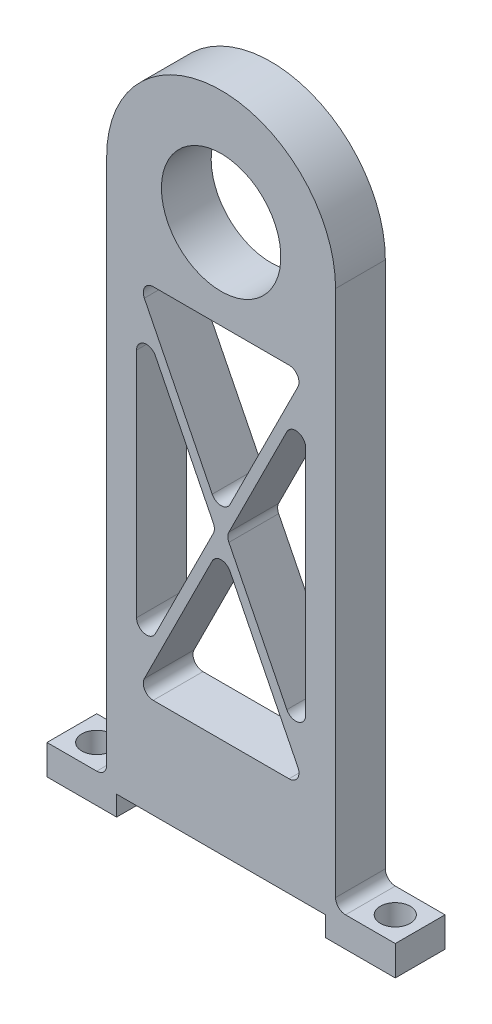
SolidWorks part; units mm, degrees
ref_plane "Front Plane" through (0, 0, 0) normal (0, 0, 1) x (1, 0, 0)
ref_plane "Top Plane" through (0, 0, 0) normal (0, 1, 0) x (1, 0, 0)
ref_plane "Right Plane" through (0, 0, 0) normal (1, 0, 0) x (0, 0, -1)
sketch "Sketch1" plane through (0, 0, 0) normal (0, 1, 0) x (1, 0, 0)
  line L1 (44.45, 6.35) -> (-44.45, 6.35)
  line L2 (44.45, 6.35) -> (44.45, -6.35)
  line L3 (44.45, -6.35) -> (-44.45, -6.35)
  line L4 (-44.45, 6.35) -> (-44.45, -6.35)
  line L5 (44.45, 6.35) -> (-44.45, -6.35) construction
  line L6 (44.45, -6.35) -> (-44.45, 6.35) construction
  line L7 (-38.1, 0) -> (-44.45, 0) construction
  line L8 (38.1, 0) -> (44.45, 0) construction
  circle A0 centre (-38.1, 0) radius 3.81
  circle A1 centre (38.1, 0) radius 3.81
  point P0 (0, 0)
  dimension "D1" = 7.62
  dimension "D2" = 76.2
  dimension "D3" = 88.9
  dimension "D4" = 12.7
extrude "Boss-Extrude1" add sketch "Sketch1" along normal blind 7.62
sketch "Sketch2" plane through (0, 7.62, 0) normal (0, 1, 0) x (1, 0, 0)
  line L0 (44.45, 6.35) -> (-44.45, 6.35) construction
  line L1 (29.21, 6.35) -> (-29.21, 6.35)
  line L2 (29.21, 6.35) -> (29.21, -6.35)
  line L3 (29.21, -6.35) -> (-29.21, -6.35)
  line L4 (-29.21, 6.35) -> (-29.21, -6.35)
  line L5 (29.21, 6.35) -> (-29.21, -6.35) construction
  line L6 (29.21, -6.35) -> (-29.21, 6.35) construction
  point P0 (0, 0)
  dimension "D1" = 58.42
extrude "Boss-Extrude2" add sketch "Sketch2" along normal blind 137.16
sketch "Sketch3" plane through (0, 0, 6.35) normal (0, 0, 1) x (1, 0, 0)
  line L0 (29.21, 144.78) -> (-29.21, 144.78)
  arc A0 (29.21, 144.78) -> (-29.21, 144.78) centre (0, 144.78) ccw
extrude "Boss-Extrude3" add sketch "Sketch3" against normal up to surface (12.7 mm away) contours A0 L0 up to face at (0, 40.005, -6.35)
sketch "Sketch4" plane through (0, 0, -6.35) normal (0, 0, -1) x (-1, 0, 0)
  line L0 (0, 144.78) -> (0, 0) construction
  line L1 (-44.45, 0) -> (44.45, 0) construction
  circle A0 centre (0, 144.78) radius 15.24
  dimension "D1" = 30.48
extrude "Cut-Extrude1" cut sketch "Sketch4" against normal up to surface (12.7 mm away) up to face at (0, 43.6562, 6.35)
sketch "Sketch5" plane through (0, 0, 6.35) normal (0, 0, 1) x (1, 0, 0)
  line L0 (-21.4401, 121.92) -> (21.4401, 121.92)
  line L1 (24.13, 27.94) -> (-24.13, 27.94)
  line L2 (24.13, 27.94) -> (24.13, 124.46)
  line L3 (24.13, 124.46) -> (-24.13, 124.46)
  line L4 (-24.13, 27.94) -> (-24.13, 124.46)
  line L5 (24.13, 27.94) -> (-24.13, 124.46) construction
  line L6 (24.13, 124.46) -> (-24.13, 27.94) construction
  line L7 (21.4401, 121.92) -> (0, 79.0398)
  line L8 (0, 79.0398) -> (-21.4401, 121.92)
  line L9 (-21.59, 116.5402) -> (-1.4199, 76.2)
  line L10 (-1.4199, 76.2) -> (-21.59, 35.8598)
  line L11 (-21.59, 35.8598) -> (-21.59, 116.5402)
  line L12 (0, 73.3602) -> (-21.4401, 30.48)
  line L13 (-21.4401, 30.48) -> (21.4401, 30.48)
  line L14 (21.4401, 30.48) -> (0, 73.3602)
  line L15 (21.59, 116.5402) -> (21.59, 35.8598)
  line L16 (21.59, 35.8598) -> (1.4199, 76.2)
  line L17 (1.4199, 76.2) -> (21.59, 116.5402)
  line L18 (-24.13, 76.2) -> (-21.59, 76.2) construction
  line L19 (24.13, 76.2) -> (21.59, 76.2) construction
  line L20 (0, 30.48) -> (0, 27.94) construction
  line L21 (0, 124.46) -> (0, 121.92) construction
  line L22 (-44.45, 0) -> (44.45, 0) construction
  line L23 (26.67, 5.08) -> (-26.67, 5.08)
  line L24 (26.67, 5.08) -> (26.67, 0)
  line L25 (26.67, 0) -> (-26.67, 0)
  line L26 (-26.67, 5.08) -> (-26.67, 0)
  line L27 (26.67, 5.08) -> (-26.67, 0) construction
  line L28 (26.67, 0) -> (-26.67, 5.08) construction
  line L29 (-29.21, 144.78) -> (-29.21, 7.62) construction
  line L30 (29.21, 144.78) -> (29.21, 7.62) construction
  line L31 (-29.21, 76.2) -> (-24.13, 76.2) construction
  line L32 (24.13, 76.2) -> (29.21, 76.2) construction
  circle A0 centre (0, 144.78) radius 15.24 construction
  point P0 (0, 76.2)
  point P23 (0, 2.54)
  point P38 (-29.21, 76.2)
  dimension "D7" = 20.32
  dimension "D1" = 2.54
  dimension "D2" = 2.54
  dimension "D3" = 5.08
  dimension "D4" = 2.54
  dimension "D5" = 2.54
  dimension "D6" = 5.08
extrude "Cut-Extrude2" cut sketch "Sketch5" against normal up to next contours L8 L0 L7 | L17 L15 L16 | L12 L13 L14 | L9 L10 L11 | L24 L23 L26 L25
fillet "Fillet1" radius 2.54 2 edges at (29.21, 7.62, 0) (-29.21, 7.62, 0)
fillet "Fillet2" radius 2.54 12 edges at (0, 73.3602, 0) (-1.4199, 76.2, 0) (0, 79.0398, 0) (1.4199, 76.2, 0) (21.59, 35.8598, 0) (21.4401, 30.48, 0) (-21.4401, 30.48, 0) (-21.59, 35.8598, 0) (-21.59, 116.5402, 0) (21.59, 116.5402, 0) (21.4401, 121.92, 0) (-21.4401, 121.92, 0)
